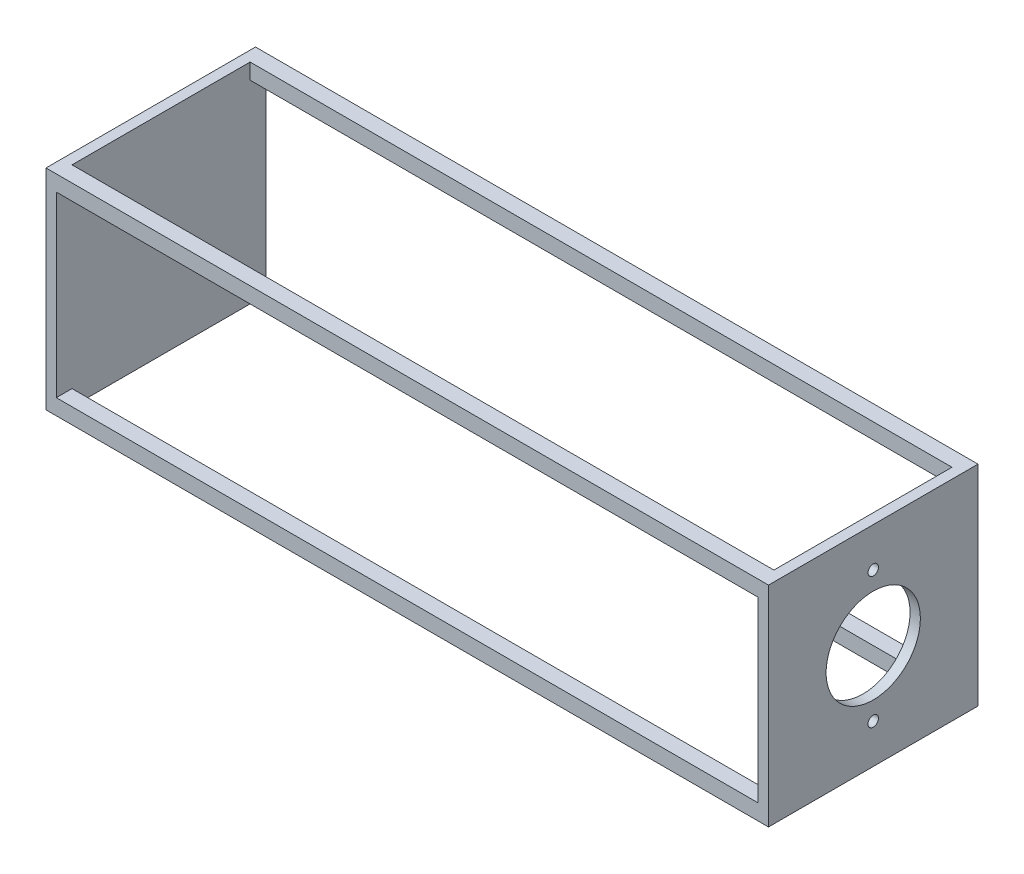
SolidWorks part; units mm, degrees
ref_plane "Front Plane" through (0, 0, 0) normal (0, 0, 1) x (1, 0, 0)
ref_plane "Top Plane" through (0, 0, 0) normal (0, 1, 0) x (1, 0, 0)
ref_plane "Right Plane" through (0, 0, 0) normal (1, 0, 0) x (0, 0, -1)
sketch "Sketch2" plane through (0, 0, 0) normal (0, 0, 1) x (1, 0, 0)
  line L4 (87.591, 25.4) -> (87.591, -25.4)
  line L5 (-87.591, 25.4) -> (-87.591, -25.4)
  line L7 (-87.591, 25.4) -> (87.591, 25.4)
  line L8 (-87.591, -25.4) -> (87.591, -25.4)
  point P1 (0, 0)
  point P7 (0, 25.4)
  dimension "D1" = 175.182
  dimension "D2" = 50.8
  dimension "D3" = 25.4
extrude "Boss-Extrude1" add sketch "Sketch2" against normal mid plane 50.8
sketch "Sketch5" plane through (0, 0, 0) normal (1, 0, 0) x (0, 0, -1)
  line L1 (-22.86, -22.86) -> (22.86, -22.86)
  line L2 (-22.86, -22.86) -> (-22.86, 22.86)
  line L3 (-22.86, 22.86) -> (22.86, 22.86)
  line L4 (22.86, -22.86) -> (22.86, 22.86)
  line L5 (-22.86, -22.86) -> (22.86, 22.86) construction
  line L6 (-22.86, 22.86) -> (22.86, -22.86) construction
  point P0 (0, 0)
  dimension "D1" = 45.72
  dimension "D2" = 45.72
sketch "Sketch8" plane through (87.591, 0, 0) normal (1, 0, 0) x (0, 0, -1)
  circle A0 centre (0, 0) radius 11.43
  circle A1 centre (0, 15.875) radius 1.27
  circle A2 centre (0, -15.875) radius 1.27
  dimension "D1" = 22.86
  dimension "D4" = 2.54
  dimension "D5" = 2.54
  dimension "D2" = 15.875
  dimension "D3" = 15.875
extrude "Cut-Extrude3" cut sketch "Sketch8" against normal blind 12.7
sketch "Sketch10" plane through (0, 25.4, 0) normal (0, 1, 0) x (1, 0, 0)
  line L1 (-85.09, 21.59) -> (85.09, 21.59)
  line L2 (-85.09, 21.59) -> (-85.09, -21.59)
  line L3 (-85.09, -21.59) -> (85.09, -21.59)
  line L4 (85.09, 21.59) -> (85.09, -21.59)
  line L5 (-85.09, 21.59) -> (85.09, -21.59) construction
  line L6 (-85.09, -21.59) -> (85.09, 21.59) construction
  point P0 (0, 0)
  dimension "D1" = 43.18
  dimension "D2" = 170.18
extrude "Cut-Extrude5" cut sketch "Sketch10" against normal through all
sketch "Sketch11" plane through (-87.591, 0, 0) normal (-1, 0, 0) x (0, 0, 1)
  circle A0 centre (0, 12.7) radius 3.175
  dimension "D1" = 6.35
  dimension "D2" = 12.7
extrude "Boss-Extrude2" add sketch "Sketch11" along normal blind 6.35
pattern_circular "CirPattern2" count 4 every 90 about axis through (0, 0, 0) along (1, 0, 0) of "Boss-Extrude2"
pattern_circular "CirPattern3" count 2 every 90 about axis through (74.891, 0, 0) along (1, 0, 0) of "Cut-Extrude5"
